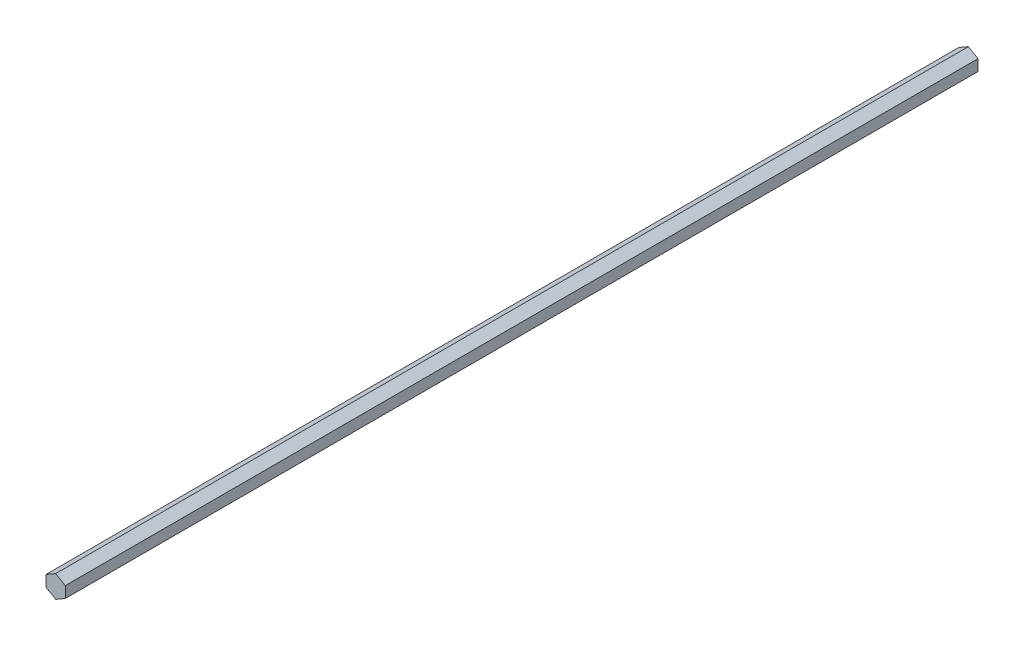
SolidWorks part; units mm, degrees
ref_plane "前视基准面" through (0, 0, 0) normal (0, 0, 1) x (1, 0, 0)
ref_plane "上视基准面" through (0, 0, 0) normal (0, 1, 0) x (1, 0, 0)
ref_plane "右视基准面" through (0, 0, 0) normal (1, 0, 0) x (0, 0, -1)
sketch "草图1" plane through (0, 0, 0) normal (0, 0, 1) x (1, 0, 0)
  line L1 (0, -5.5) -> (4.7631, -2.75)
  line L2 (4.7631, -2.75) -> (4.7631, 2.75)
  line L3 (4.7631, 2.75) -> (0, 5.5)
  line L4 (0, 5.5) -> (-4.7631, 2.75)
  line L5 (-4.7631, 2.75) -> (-4.7631, -2.75)
  line L6 (-4.7631, -2.75) -> (0, -5.5)
  circle A0 centre (0, 0) radius 5.5 construction
  dimension "D1" = 11
extrude "凸台-拉伸1" add sketch "草图1" along normal blind 450
